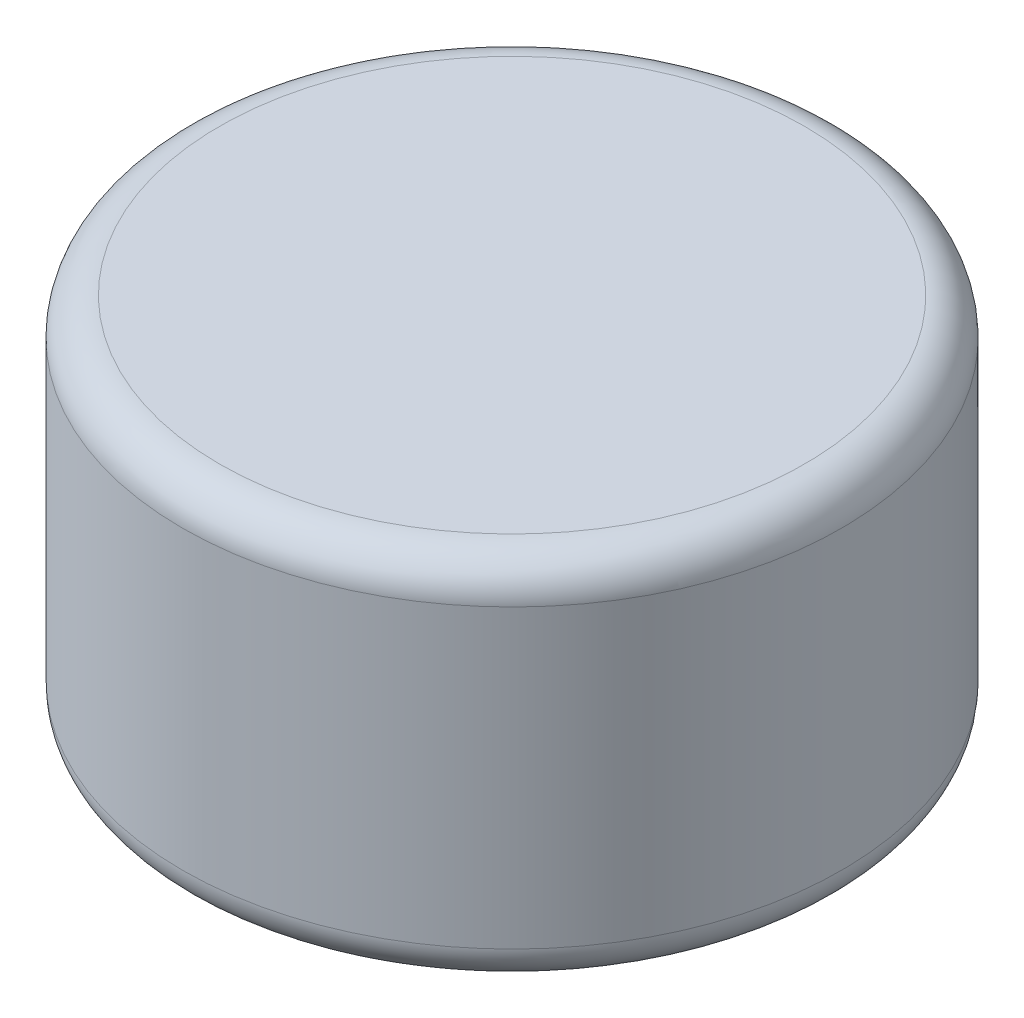
SolidWorks part; units mm, degrees
other "相机1"
other "相机2"
material "PEN"
ref_plane "前视基准面" through (0, 0, 0) normal (0, 0, 1) x (1, 0, 0)
ref_plane "上视基准面" through (0, 0, 0) normal (0, 1, 0) x (1, 0, 0)
ref_plane "右视基准面" through (0, 0, 0) normal (1, 0, 0) x (0, 0, -1)
sketch "草图1" plane through (0, 0, 0) normal (0, 1, 0) x (1, 0, 0)
  circle A0 centre (0, 0) radius 44.5
extrude "凸台-拉伸1" add sketch "草图1" along normal mid plane 50
fillet "圆角1" radius 5 2 edges at (0, -25, 44.5) (0, 25, 44.5)
sketch "草图9" plane through (0, 0, 0) normal (0, 1, 0) x (1, 0, 0)
  circle A0 centre (0, 0) radius 40.5
extrude "切除-拉伸1" cut sketch "草图9" against normal mid plane 40.1
